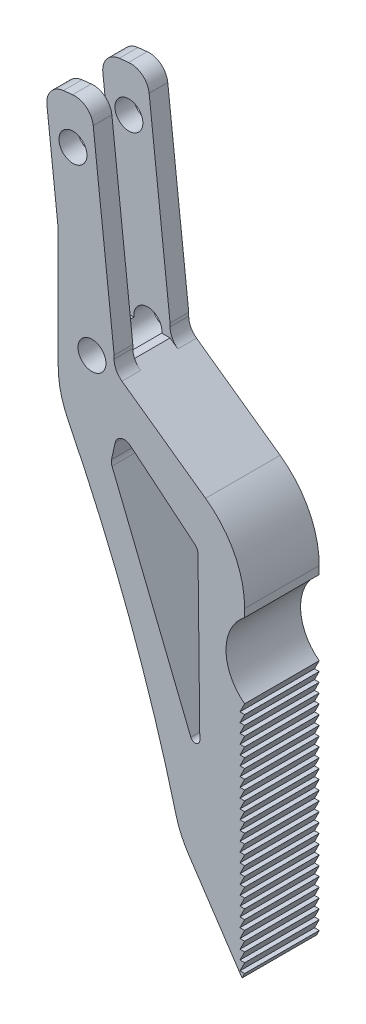
SolidWorks part; units mm, degrees
ref_plane "Front Plane" through (0, 0, 0) normal (0, 0, 1) x (1, 0, 0)
ref_plane "Top Plane" through (0, 0, 0) normal (0, 1, 0) x (1, 0, 0)
ref_plane "Right Plane" through (0, 0, 0) normal (1, 0, 0) x (0, 0, -1)
sketch "Sketch1" plane through (0, 0, 0) normal (0, 0, 1) x (1, 0, 0)
  line L0 (0, 0) -> (-20, 30.0054)
  line L1 (-20, 30.0054) -> (-20, 60.1354)
  line L2 (-20, 60.1354) -> (-21.4356, 73.0559)
  line L3 (-21.4356, 73.0559) -> (-16.4661, 73.608)
  line L4 (-16.4661, 73.608) -> (-14.0003, 51.4146)
  line L5 (-14.0003, 51.4146) -> (-14.0003, 50.0146)
  line L6 (-14.0003, 50.0146) -> (0, 40.0283)
  line L7 (0, 40.0283) -> (0, 0)
  dimension "D1" = 20
  dimension "D2" = 36.06
  dimension "D3" = 30.13
  dimension "D4" = 13
  dimension "D5" = 186.34
  dimension "D6" = 5
  dimension "D7" = 22.33
  dimension "D8" = 1.4
  dimension "D9" = 173.66
  dimension "D10" = 125.5
extrude "Boss-Extrude1" add sketch "Sketch1" along normal mid plane 8
sketch "Sketch2" plane through (0, 0, 0) normal (0, 0, 1) x (1, 0, 0)
  line L1 (-14.0003, 50.0146) -> (-34.0003, 50.0146)
  line L2 (-14.0003, 50.0146) -> (-14.0003, 75.0146)
  line L3 (-14.0003, 75.0146) -> (-34.0003, 75.0146)
  line L4 (-34.0003, 50.0146) -> (-34.0003, 75.0146)
  dimension "D1" = 20
  dimension "D2" = 25
extrude "Cut-Extrude1" cut sketch "Sketch2" against normal mid plane 4
sketch "Sketch3" plane through (0, 0, 4) normal (0, 0, 1) x (1, 0, 0)
  line L2 (0, 0) -> (0, 40.0283) construction
  arc A0 (0, 34.0283) -> (0, 26.0283) centre (3, 30.0283) ccw
  point P3 (0, 0)
  point P7 (0, 0)
  point P8 (0, 0)
  dimension "D1" = 5
  dimension "D2" = 6
  dimension "D3" = 10
extrude "Cut-Extrude2" cut sketch "Sketch3" against normal through all and the other way through all
sketch "Sketch4" plane through (0, 0, 4) normal (0, 0, 1) x (1, 0, 0)
  line L0 (0, 26.0283) -> (-0.5, 25.0283)
  line L1 (-0.5, 25.0283) -> (0, 25.0283)
  line L2 (0, 0) -> (0, 26.0283) construction
  line L3 (0, 26.0283) -> (0, 25.0283)
  dimension "D1" = 1
  dimension "D2" = 0.5
extrude "Cut-Extrude3" cut sketch "Sketch4" against normal through all
pattern_linear "LPattern2" count 26 spacing 1.0025 along (0, -1, 0) of "Cut-Extrude3"
sketch "Sketch5" plane through (0, 0, 4) normal (0, 0, 1) x (1, 0, 0)
  line L0 (-20, 60.1354) -> (-20, 30.0054) construction
  line L1 (-20, 30.0054) -> (-0.2759, 0.414) construction
  line L2 (-20, 30.0054) -> (-6.9551, 10.4345)
  line L3 (-20, 45.0054) -> (-20, 30.0054)
  arc A0 (-20, 45.0054) -> (-6.9551, 10.4345) centre (-162.1735, -28.3887) cw
  dimension "D3" = 160
  dimension "D1" = 15
  dimension "D2" = 23.52
extrude "Cut-Extrude4" cut sketch "Sketch5" against normal through all
sketch "Sketch6" plane through (0, 0, 4) normal (0, 0, 1) x (1, 0, 0)
  line L0 (-13.5444, 44.9324) -> (-5.0102, 37.8974)
  line L1 (-5.0102, 37.8974) -> (-4.7792, 17.5724)
  line L2 (-13.5444, 44.9324) -> (-14.3459, 41.2724)
  line L3 (0, 40.0283) -> (-14.0003, 50.0146) construction
  line L4 (0, 34.0283) -> (0, 40.0283) construction
  spline S1 degree 1 poles (-4.7792, 17.5724) (-14.3459, 41.2724) knots 0 0 1 1
  point P8 (0, 37.0283)
  point P9 (0, 0)
  dimension "D1" = 4
  dimension "D2" = 5
  dimension "D3" = 3.66
  dimension "D4" = 23.7
  dimension "D5" = 11.06
extrude "Cut-Extrude5" cut sketch "Sketch6" against normal through all
fillet "Fillet1" radius 10 3 edges at (-20, 45.0054, 0) (-6.9551, 10.4345, 0) (0, 40.0283, 0)
fillet "Fillet2" radius 2 6 edges at (-14.0003, 50.0146, 3) (-14.0003, 50.0146, -3) (-16.4661, 73.608, 3) (-16.4661, 73.608, -3) (-21.4356, 73.0559, -3) (-21.4356, 73.0559, 3)
fillet "Fillet3" radius 1 3 edges at (-14.3459, 41.2724, 0) (-5.0102, 37.8974, 0) (-13.5444, 44.9324, 0)
fillet "Fillet4" radius 0.5 1 edges at (-4.7792, 17.5724, 0)
sketch "Sketch7" plane through (0, 0, 4) normal (0, 0, 1) x (1, 0, 0)
  line L0 (-18.9509, 73.332) -> (-16.3899, 50.2827) construction
  line L1 (-18.4539, 73.3872) -> (-19.4478, 73.2767) construction
  line L2 (-14.0003, 51.4146) -> (-16.2453, 71.6203) construction
  circle A0 centre (-18.4164, 68.5216) radius 1.5
  circle A1 centre (-16.3812, 50.2043) radius 1.5
  dimension "D1" = 3
  dimension "D2" = 3
  dimension "D3" = 18.43
  dimension "D4" = 4.84
extrude "Cut-Extrude6" cut sketch "Sketch7" against normal through all
